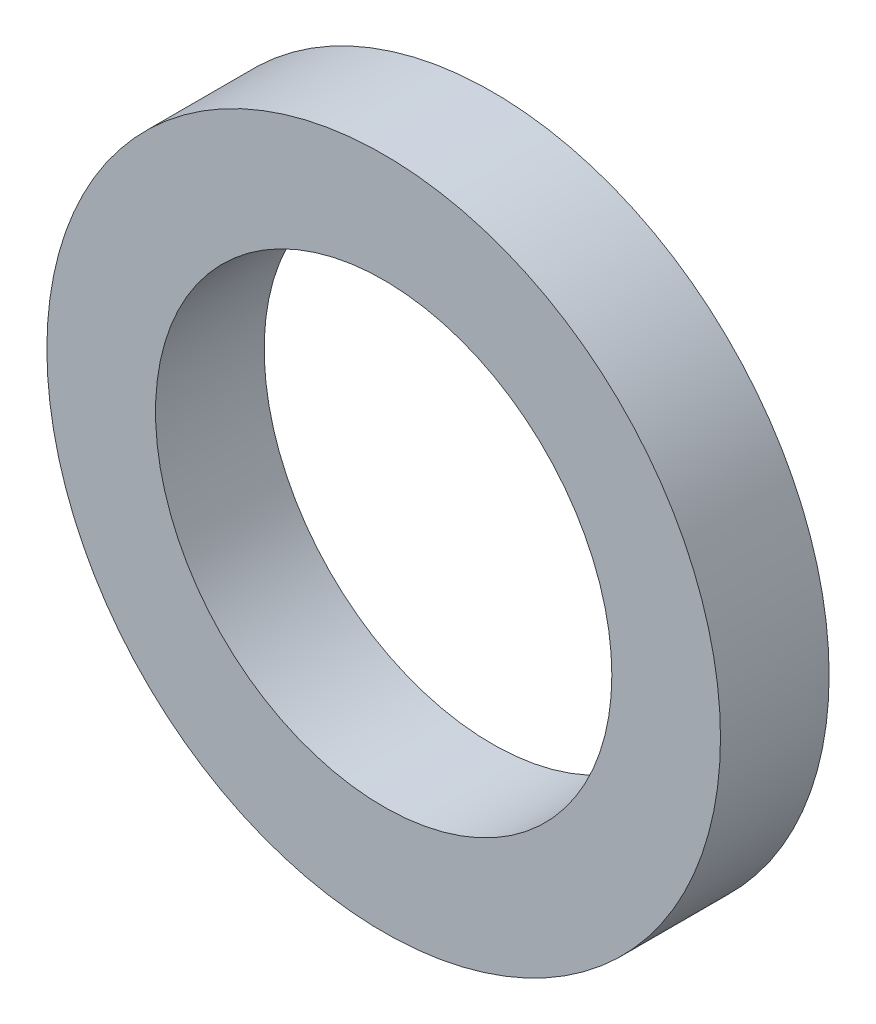
SolidWorks part; units mm, degrees
ref_plane "Front Plane" through (0, 0, 0) normal (0, 0, 1) x (1, 0, 0)
ref_plane "Top Plane" through (0, 0, 0) normal (0, 1, 0) x (1, 0, 0)
ref_plane "Right Plane" through (0, 0, 0) normal (1, 0, 0) x (0, 0, -1)
sketch "Sketch1" plane through (0, 0, 0) normal (0, 0, 1) x (1, 0, 0)
  circle A0 centre (0, 0) radius 3.1
  circle A1 centre (0, 0) radius 2.1
  dimension "D1" = 6.2
  dimension "D2" = 4.2
extrude "Boss-Extrude1" add sketch "Sketch1" along normal blind 1
